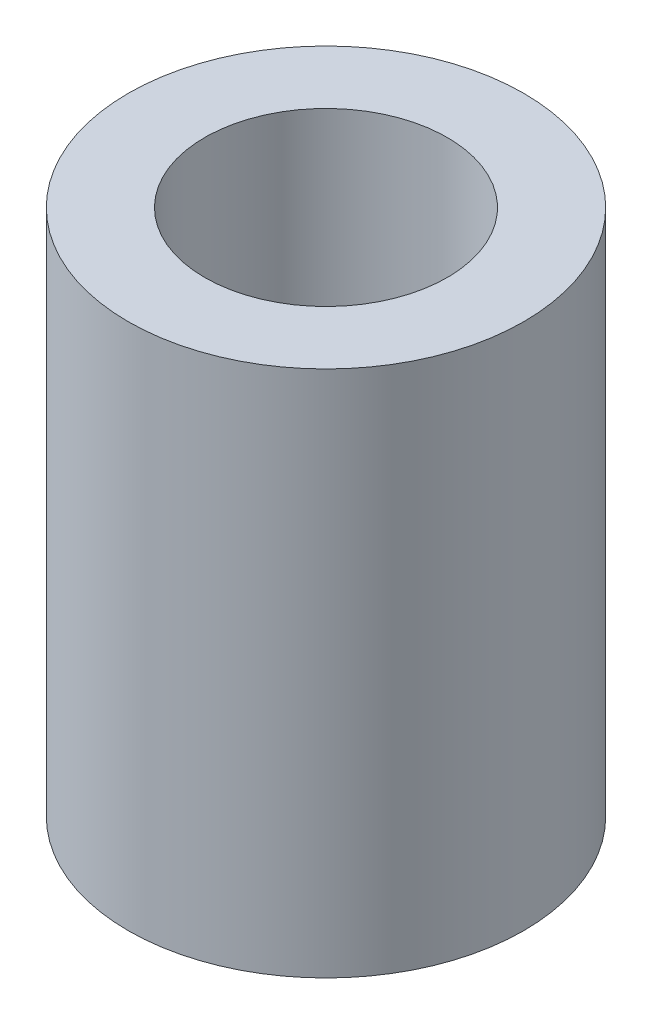
SolidWorks part; units mm, degrees
ref_plane "Front Plane" through (0, 0, 0) normal (0, 0, 1) x (1, 0, 0)
ref_plane "Top Plane" through (0, 0, 0) normal (0, 1, 0) x (1, 0, 0)
ref_plane "Right Plane" through (0, 0, 0) normal (1, 0, 0) x (0, 0, -1)
sketch "Sketch1" plane through (0, 0, 0) normal (0, 1, 0) x (1, 0, 0)
  circle A0 centre (0, 0) radius 1.4605
  circle A1 centre (0, 0) radius 2.3813
  dimension "D1" = 2.921
  dimension "D2" = 4.7625
extrude "Boss-Extrude1" add sketch "Sketch1" along normal blind 6.35
